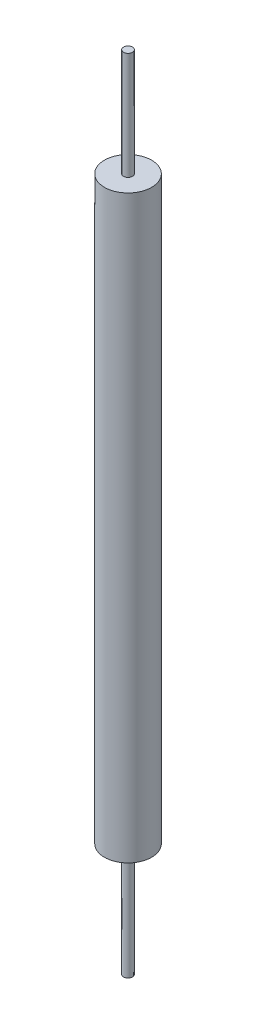
SolidWorks part; units mm, degrees
ref_plane "Front Plane" through (0, 0, 0) normal (0, 0, 1) x (1, 0, 0)
ref_plane "Top Plane" through (0, 0, 0) normal (0, 1, 0) x (1, 0, 0)
ref_plane "Right Plane" through (0, 0, 0) normal (1, 0, 0) x (0, 0, -1)
sketch "Sketch1" plane through (0, 0, 0) normal (0, 1, 0) x (1, 0, 0)
  circle A0 centre (0, 0) radius 25
  dimension "D1" = 50
extrude "Boss-Extrude1" add sketch "Sketch1" along normal blind 789.6
sketch "Sketch2" plane through (0, 789.6, 0) normal (0, 1, 0) x (1, 0, 0)
  circle A0 centre (0, 0) radius 4.7625
  circle A2 centre (0, 0) radius 25
  dimension "D1" = 9.525
  dimension "D2" = 50
extrude "Cut-Extrude1" cut sketch "Sketch2" against normal blind 74
sketch "Sketch3" plane through (0, 0, 0) normal (0, -1, 0) x (1, 0, 0)
  circle A0 centre (0, 0) radius 4.7625
  circle A1 centre (0, 0) radius 25
  dimension "D1" = 9.525
  dimension "D2" = 50
extrude "Cut-Extrude2" cut sketch "Sketch3" against normal blind 100
sketch "Sketch4" plane through (0, 0, 0) normal (1, 0, 0) x (0, 0, -1)
  circle A0 centre (3.5707, 337.95) radius 1.5
  dimension "D1" = 3
extrude "Cut-Extrude3" cut sketch "Sketch4" against normal blind 30
sketch "Sketch5" plane through (0, 0, 0) normal (0, -1, 0) x (1, 0, 0)
  circle A0 centre (0, 0) radius 4.7625
extrude "Boss-Extrude3" add sketch "Sketch5" along normal blind 20
sketch "Sketch6" plane through (0, 789.6, 0) normal (0, 1, 0) x (1, 0, 0)
  circle A0 centre (0, 0) radius 4.7625
extrude "Boss-Extrude4" add sketch "Sketch6" along normal blind 40
